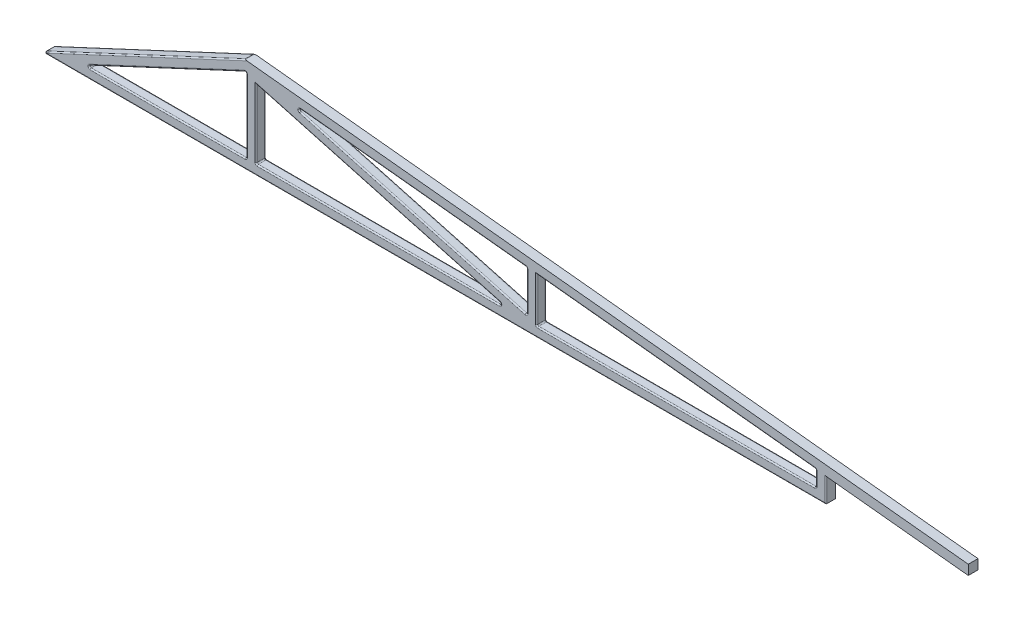
SolidWorks part; units mm, degrees
ref_plane "Front Plane" through (0, 0, 0) normal (0, 0, 1) x (1, 0, 0)
ref_plane "Top Plane" through (0, 0, 0) normal (0, 1, 0) x (1, 0, 0)
ref_plane "Right Plane" through (0, 0, 0) normal (1, 0, 0) x (0, 0, -1)
sketch "Sketch1" plane through (0, 0, 0) normal (0, 0, 1) x (1, 0, 0)
  line L0 (0, 0) -> (838.3347, 390.9219)
  line L1 (838.3347, 390.9219) -> (3817.1747, 80.217)
  line L2 (3230, 0) -> (0, 0)
  line L3 (885.2012, 345.8165) -> (1999.8658, 229.5526)
  line L5 (180.4283, 40) -> (845.2012, 349.9887)
  line L6 (3230, 101.2447) -> (3230, 40)
  line L7 (3190, 105.4168) -> (3190, 40)
  line L8 (3230, 40) -> (3230, 0)
  line L9 (3190, 40) -> (2039.8658, 40)
  line L10 (3817.1747, 40) -> (180.4283, 40) construction
  line L11 (4586.244, 0) -> (0, 0) construction
  line L12 (3817.1747, 40) -> (3817.1747, 80.217)
  line L13 (838.3347, 390.9219) -> (4586.244, 0) construction
  line L14 (845.2012, 349.9887) -> (845.2012, 40)
  line L15 (885.2012, 345.8165) -> (885.2012, 40)
  line L16 (845.2012, 349.9887) -> (3817.1747, 40) construction
  line L17 (845.2012, 40) -> (180.4283, 40)
  line L18 (885.2012, 349.9887) -> (885.2012, 40) construction
  line L19 (1999.8658, 229.5526) -> (1999.8658, 40)
  line L20 (2039.8658, 225.3804) -> (2039.8658, 40)
  line L21 (2039.8658, 229.5526) -> (2039.8658, 40) construction
  line L22 (2039.8658, 225.3804) -> (3190, 105.4168)
  line L23 (1999.8658, 40) -> (885.2012, 40)
  line L24 (3190, 101.2447) -> (3190, 40) construction
  line L25 (885.2012, 325.0775) -> (1924.2744, 40)
  line L26 (1007.1574, 333.096) -> (1999.8658, 60.7391)
  line L27 (3230, 101.2447) -> (3817.1747, 40)
  dimension "D1" = 925
  dimension "D2" = 2995
  dimension "D3" = 25
  dimension "D6" = 3230
  dimension "D4" = 40
  dimension "D5" = 40
  dimension "D7" = 40
  dimension "D8" = 40
extrude "Boss-Extrude1" add sketch "Sketch1" along normal blind 40 contours L6 L27 L12 L1 L0 L2 L8 L19 L23 L15 L3 L20 L22 L7 L9 L14 L17 L5 | L26 L3 L15 L25 L23 L19
fillet "Fillet1" radius 5 43 edges at (1404.7378, 182.5387, 0) (885.2012, 182.5387, 0) (1503.5116, 281.3243, 0) (2614.9329, 165.3986, 0) (2039.8658, 132.6902, 0) (512.8148, 194.9943, 0) (1404.7378, 40, 0) (1999.8658, 145.1458, 0) (1503.5116, 196.9175, 0) (3190, 72.7084, 0) (2614.9329, 40, 0) (845.2012, 194.9943, 0) (512.8148, 40, 0) (419.1674, 195.4609, 0) (1404.7378, 182.5387, 40) (1404.7378, 40, 40) (885.2012, 182.5387, 40) (1999.8658, 145.1458, 40) (1503.5116, 196.9175, 40) (1503.5116, 281.3243, 40) (2039.8658, 132.6902, 40) (2614.9329, 165.3986, 40) (3190, 72.7084, 40) (2614.9329, 40, 40) (845.2012, 194.9943, 40) (512.8148, 40, 40) (512.8148, 194.9943, 40) (3230, 50.6223, 40) (419.1674, 195.4609, 40) (1615, 0, 40) (885.2012, 40, 20) (1924.2744, 40, 20) (1999.8658, 229.5526, 20) (1007.1574, 333.096, 20) (1999.8658, 60.7391, 20) (2039.8658, 40, 20) (3190, 40, 20) (3190, 105.4168, 20) (845.2012, 349.9887, 20) (180.4283, 40, 20) (845.2012, 40, 20) (0, 0, 20) (838.3347, 390.9219, 20)
